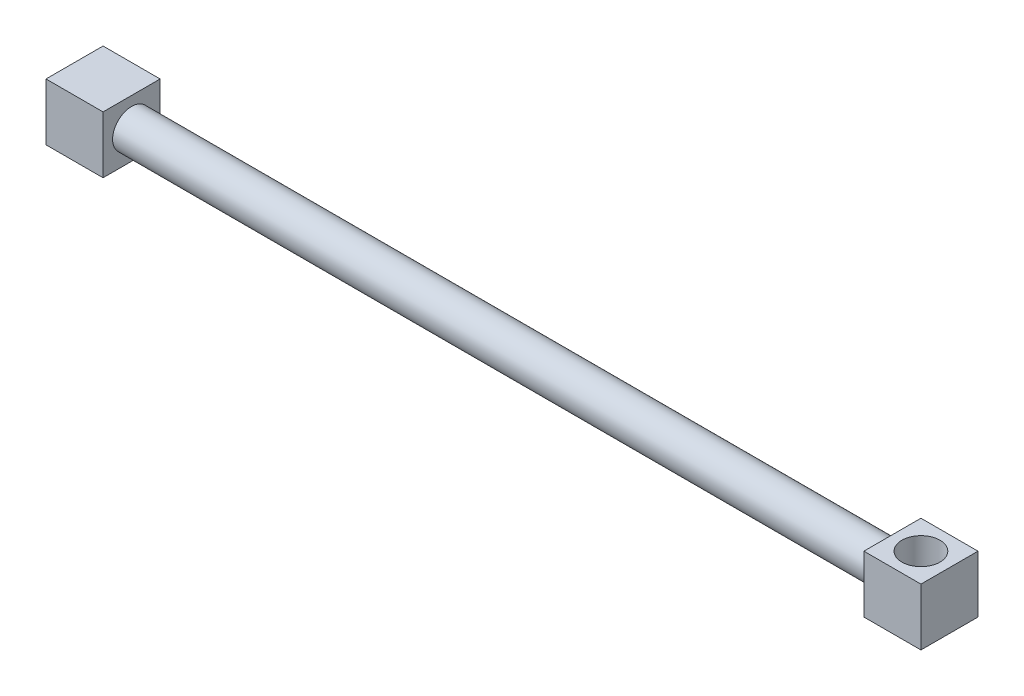
SolidWorks part; units mm, degrees
ref_plane "Front Plane" through (0, 0, 0) normal (0, 0, 1) x (1, 0, 0)
ref_plane "Top Plane" through (0, 0, 0) normal (0, 1, 0) x (1, 0, 0)
ref_plane "Right Plane" through (0, 0, 0) normal (1, 0, 0) x (0, 0, -1)
sketch "Sketch1" plane through (0, 0, 0) normal (1, 0, 0) x (0, 0, -1)
  line L1 (-15, 15) -> (15, 15)
  line L2 (-15, 15) -> (-15, -15)
  line L3 (-15, -15) -> (15, -15)
  line L4 (15, 15) -> (15, -15)
  line L5 (-15, 15) -> (15, -15) construction
  line L6 (-15, -15) -> (15, 15) construction
  point P0 (0, 0)
  dimension "D1" = 30
  dimension "D2" = 30
extrude "Boss-Extrude1" add sketch "Sketch1" along normal blind 30
sketch "Sketch2" plane through (30, 0, 0) normal (1, 0, 0) x (0, 0, -1)
  circle A0 centre (0, 0) radius 10
  dimension "D1" = 20
extrude "Boss-Extrude2" add sketch "Sketch2" along normal blind 400
sketch "Sketch3" plane through (430, 0, 0) normal (1, 0, 0) x (0, 0, -1)
  line L1 (-15, -15) -> (15, -15)
  line L2 (-15, -15) -> (-15, 15)
  line L3 (-15, 15) -> (15, 15)
  line L4 (15, -15) -> (15, 15)
  line L5 (-15, -15) -> (15, 15) construction
  line L6 (-15, 15) -> (15, -15) construction
  point P0 (0, 0)
  dimension "D1" = 30
  dimension "D2" = 30
extrude "Boss-Extrude3" add sketch "Sketch3" along normal blind 30
sketch "Sketch4" plane through (0, 15, 0) normal (0, 1, 0) x (1, 0, 0)
  line L0 (430, 15) -> (430, -15) construction
  line L2 (460, 15) -> (430, 15) construction
  circle A0 centre (445, 0) radius 10
  dimension "D1" = 20
  dimension "D2" = 15
  dimension "D3" = 15
extrude "Cut-Extrude1" cut sketch "Sketch4" against normal up to surface (30 mm away) up to face at (445, -15, 0)
